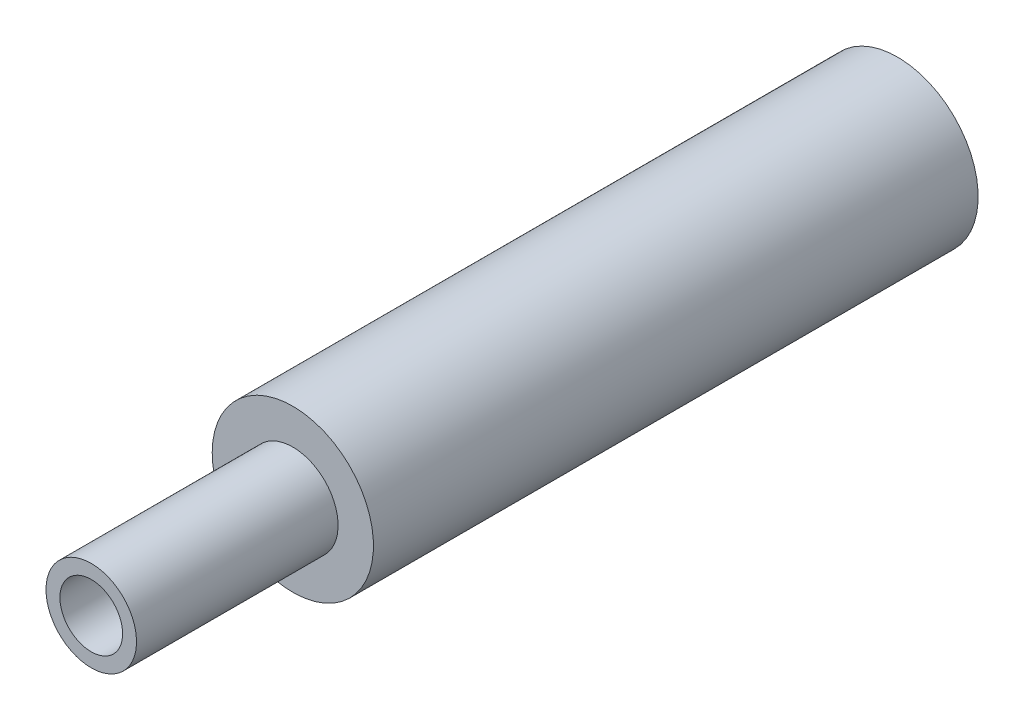
SolidWorks part; units mm, degrees
ref_plane "Front Plane" through (0, 0, 0) normal (0, 0, 1) x (1, 0, 0)
ref_plane "Top Plane" through (0, 0, 0) normal (0, 1, 0) x (1, 0, 0)
ref_plane "Right Plane" through (0, 0, 0) normal (1, 0, 0) x (0, 0, -1)
ref_plane "Plane1" through (0, 0, 0) normal (0, -1, 0) x (1, 0, 0)
sketch "Sketch1" plane through (0, 0, 0) normal (0, -1, 0) x (1, 0, 0)
  line L0 (0.7777, 17) -> (0, 17)
  line L1 (0, 17) -> (0, 10)
  line L2 (0, 10) -> (1.475, 10)
  line L3 (1.475, 10) -> (1.475, 0)
  line L4 (1.475, 0) -> (2, 0)
  line L5 (2, 0) -> (2, 15)
  line L6 (2, 15) -> (1.1226, 15)
  line L7 (1.1226, 15) -> (1.1226, 20)
  line L8 (1.1226, 20) -> (0.7777, 20)
  line L9 (0.7777, 20) -> (0.7777, 17)
  line L10 (0, 20) -> (0, 0) construction
  dimension "D1" = 0.7777
  dimension "D2" = 1.1226
  dimension "D3" = 1.475
  dimension "D4" = 2
  dimension "D5" = 10
  dimension "D6" = 15
  dimension "D7" = 17
  dimension "D8" = 20
revolve "Revolve1" add sketch "Sketch1" angle 360 about L10
